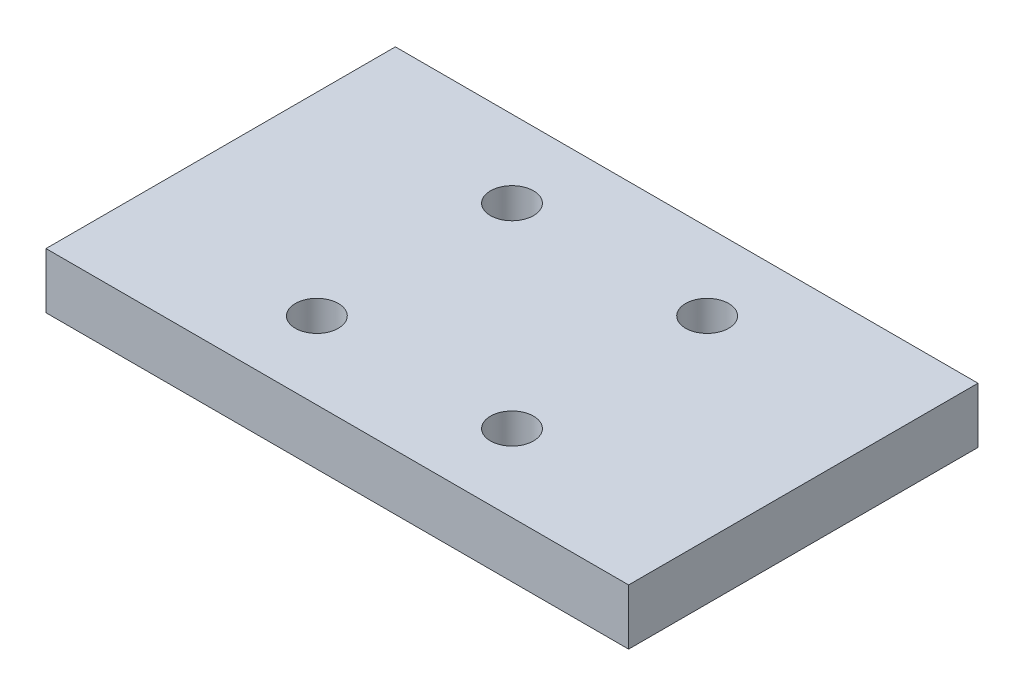
SolidWorks part; units mm, degrees
material "AISI 1045 Steel, cold drawn"
ref_plane "Front Plane" through (0, 0, 0) normal (0, 0, 1) x (1, 0, 0)
ref_plane "Top Plane" through (0, 0, 0) normal (0, 1, 0) x (1, 0, 0)
ref_plane "Right Plane" through (0, 0, 0) normal (1, 0, 0) x (0, 0, -1)
sketch "Sketch1" plane through (0, 0, 0) normal (0, 1, 0) x (1, 0, 0)
  line L1 (-33.2503, 19.939) -> (33.2503, 19.939)
  line L2 (-33.2503, 19.939) -> (-33.2503, -19.939)
  line L3 (-33.2503, -19.939) -> (33.2503, -19.939)
  line L4 (33.2503, 19.939) -> (33.2503, -19.939)
  line L5 (-33.2503, 19.939) -> (33.2503, -19.939) construction
  line L6 (-33.2503, -19.939) -> (33.2503, 19.939) construction
  circle A0 centre (0, 0) radius 19.939 construction
  dimension "D1" = 39.878
extrude "Boss-Extrude1" add sketch "Sketch1" along normal blind 6.35
hole_wizard "#10 (0.1935) Diameter Hole1" positions "Sketch2" profile "Sketch4" hole size "#10" standard "ANSI Inch" end condition through all
sketch "Sketch2" plane through (0, 0, 0) normal (0, -1, 0) x (-1, 0, 0)
  line L1 (-11.1369, 11.1369) -> (11.1369, 11.1369) construction
  line L2 (-11.1369, 11.1369) -> (-11.1369, -11.1369) construction
  line L3 (-11.1369, -11.1369) -> (11.1369, -11.1369) construction
  line L4 (11.1369, 11.1369) -> (11.1369, -11.1369) construction
  point P0 (-11.1369, 11.1369)
  point P3 (11.1369, 11.1369)
  point P6 (11.1369, -11.1369)
  point P9 (-11.1369, -11.1369)
sketch "Sketch4" plane through (11.1369, 0, -11.1369) normal (1, 0, 0) x (0, 0, -1)
  line L0 (0, 0) -> (0, 6.35)
  line L1 (0, 6.35) -> (2.4574, 6.35)
  line L2 (2.4574, 6.35) -> (2.4574, 0.635)
  line L3 (2.4574, 0.635) -> (3.0924, 0)
  line L5 (3.0924, 0) -> (0, 0)
  line L6 (-2.4574, 0.635) -> (-3.0924, 0) construction
  line L11 (0, -6.35) -> (0, 107.95) construction
  dimension "Thru Hole Dia." = 4.9149
  dimension "Thru Hole Depth" = 6.35
  dimension "Near C'Sink Dia." = 6.1849
  dimension "Near C'Sink Angle" = 90
